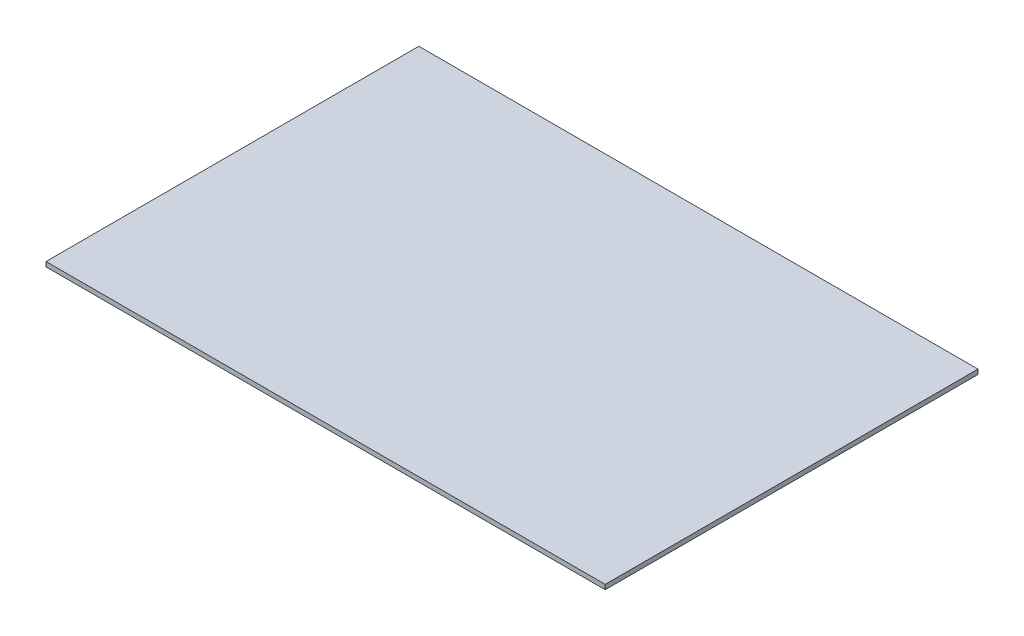
SolidWorks part; units mm, degrees
ref_plane "Front Plane" through (0, 0, 0) normal (0, 0, 1) x (1, 0, 0)
ref_plane "Top Plane" through (0, 0, 0) normal (0, 1, 0) x (1, 0, 0)
ref_plane "Right Plane" through (0, 0, 0) normal (1, 0, 0) x (0, 0, -1)
sketch "Sketch1" plane through (0, 0, 0) normal (0, 1, 0) x (1, 0, 0)
  line L1 (0, 0) -> (12000, 0)
  line L2 (0, 0) -> (0, 8000)
  line L3 (0, 8000) -> (12000, 8000)
  line L4 (12000, 0) -> (12000, 8000)
extrude "Boss-Extrude1" add sketch "Sketch1" along normal blind 100
